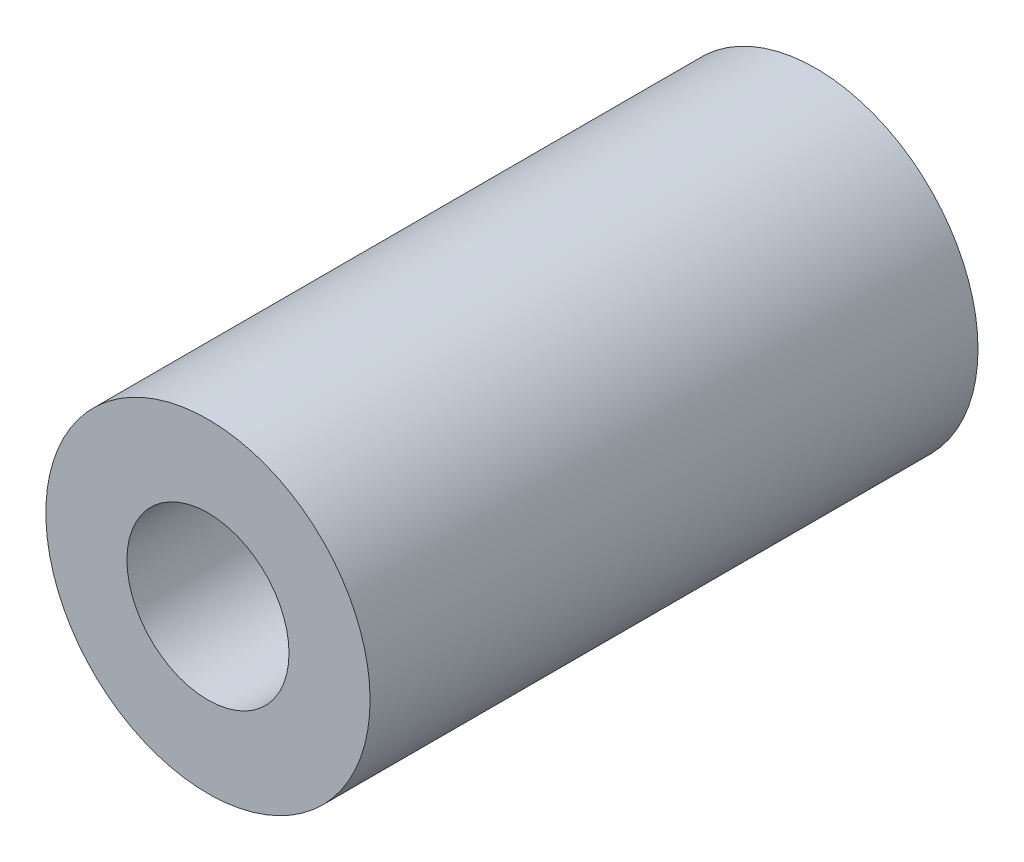
SolidWorks part; units mm, degrees
ref_plane "前视基准面" through (0, 0, 0) normal (0, 0, 1) x (1, 0, 0)
ref_plane "上视基准面" through (0, 0, 0) normal (0, 1, 0) x (1, 0, 0)
ref_plane "右视基准面" through (0, 0, 0) normal (1, 0, 0) x (0, 0, -1)
sketch "草图1" plane through (0, 0, 0) normal (0, 0, 1) x (1, 0, 0)
  circle A0 centre (0, 0) radius 4
  circle A1 centre (0, 0) radius 2
  dimension "D1" = 4
  dimension "D2" = 8
extrude "凸台-拉伸1" add sketch "草图1" along normal mid plane 15
